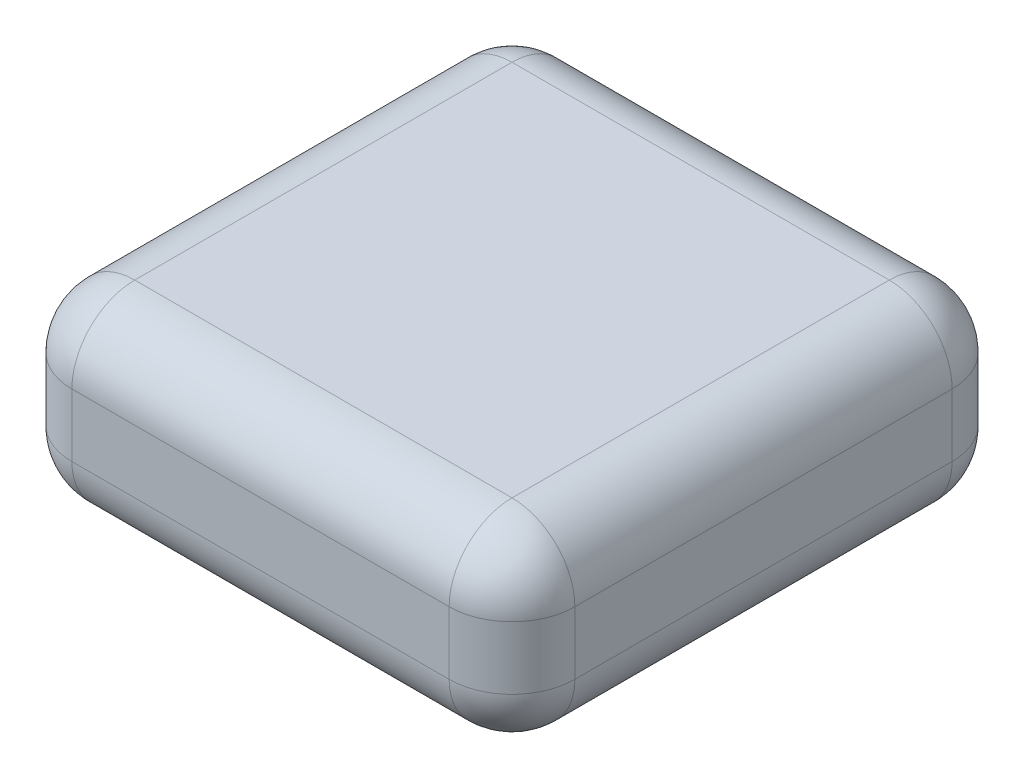
SolidWorks part; units mm, degrees
ref_plane "Front Plane" through (0, 0, 0) normal (0, 0, 1) x (1, 0, 0)
ref_plane "Top Plane" through (0, 0, 0) normal (0, 1, 0) x (1, 0, 0)
ref_plane "Right Plane" through (0, 0, 0) normal (1, 0, 0) x (0, 0, -1)
sketch "Sketch1" plane through (0, 0, 0) normal (0, 1, 0) x (1, 0, 0)
  line L1 (-609.6, 609.6) -> (609.6, 609.6)
  line L2 (-609.6, 609.6) -> (-609.6, -609.6)
  line L3 (-609.6, -609.6) -> (609.6, -609.6)
  line L4 (609.6, 609.6) -> (609.6, -609.6)
  line L5 (-609.6, 609.6) -> (609.6, -609.6) construction
  line L6 (-609.6, -609.6) -> (609.6, 609.6) construction
  point P0 (0, 0)
  dimension "D1" = 1219.2
  dimension "D2" = 1219.2
extrude "Boss-Extrude1" add sketch "Sketch1" along normal blind 457.2
fillet "Fillet1" radius 152.4 12 edges at (-609.6, 0, 0) (609.6, 0, 0) (-609.6, 457.2, 0) (609.6, 457.2, 0) (609.6, 228.6, -609.6) (0, 457.2, -609.6) (-609.6, 228.6, -609.6) (0, 0, -609.6) (-609.6, 228.6, 609.6) (0, 457.2, 609.6) (609.6, 228.6, 609.6) (0, 0, 609.6)
